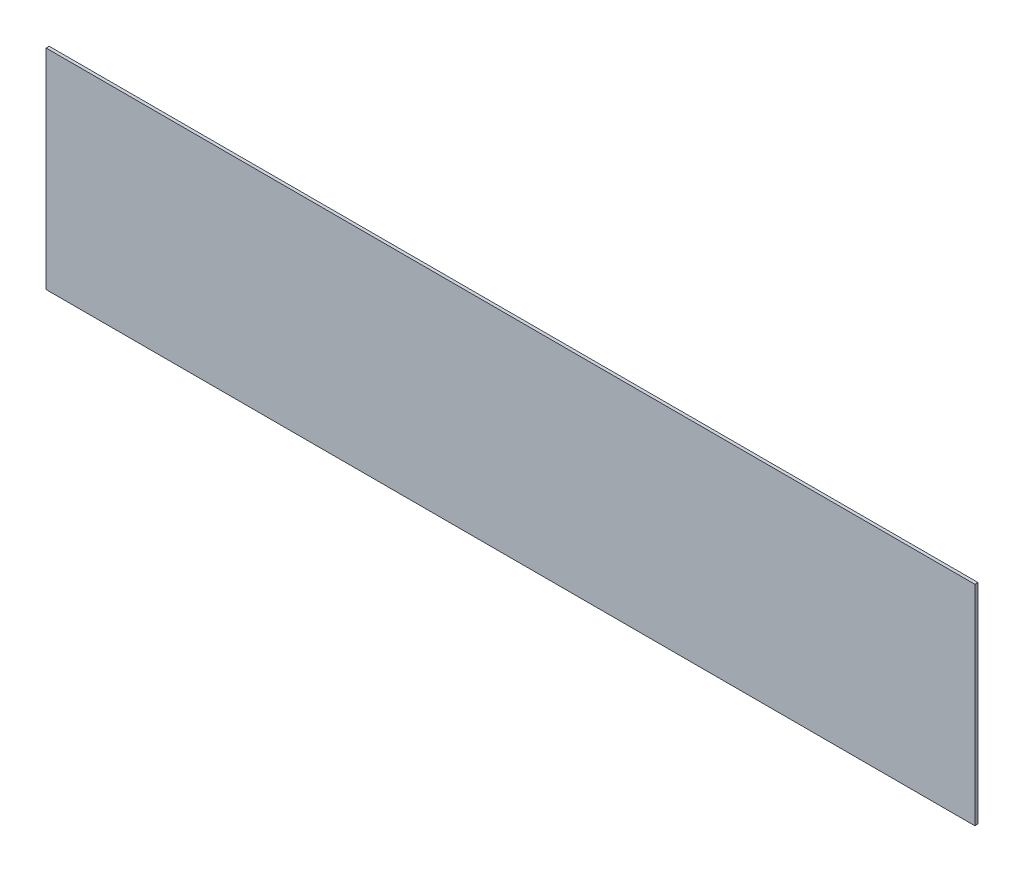
SolidWorks part; units mm, degrees
material "Acrílico (médio-alto impacto)"
ref_plane "Plano frontal" through (0, 0, 0) normal (0, 0, 1) x (1, 0, 0)
ref_plane "Plano superior" through (0, 0, 0) normal (0, 1, 0) x (1, 0, 0)
ref_plane "Plano direito" through (0, 0, 0) normal (1, 0, 0) x (0, 0, -1)
sketch "Esboço1" plane through (0, 0, 0) normal (0, 0, 1) x (1, 0, 0)
  line L1 (-599.5, -135) -> (599.5, -135)
  line L2 (-599.5, -135) -> (-599.5, 135)
  line L3 (-599.5, 135) -> (599.5, 135)
  line L4 (599.5, -135) -> (599.5, 135)
  line L5 (-599.5, -135) -> (599.5, 135) construction
  line L6 (-599.5, 135) -> (599.5, -135) construction
  point P0 (0, 0)
  dimension "D1" = 1199
  dimension "D2" = 270
extrude "Ressalto-extrusão1" add sketch "Esboço1" along normal blind 4
